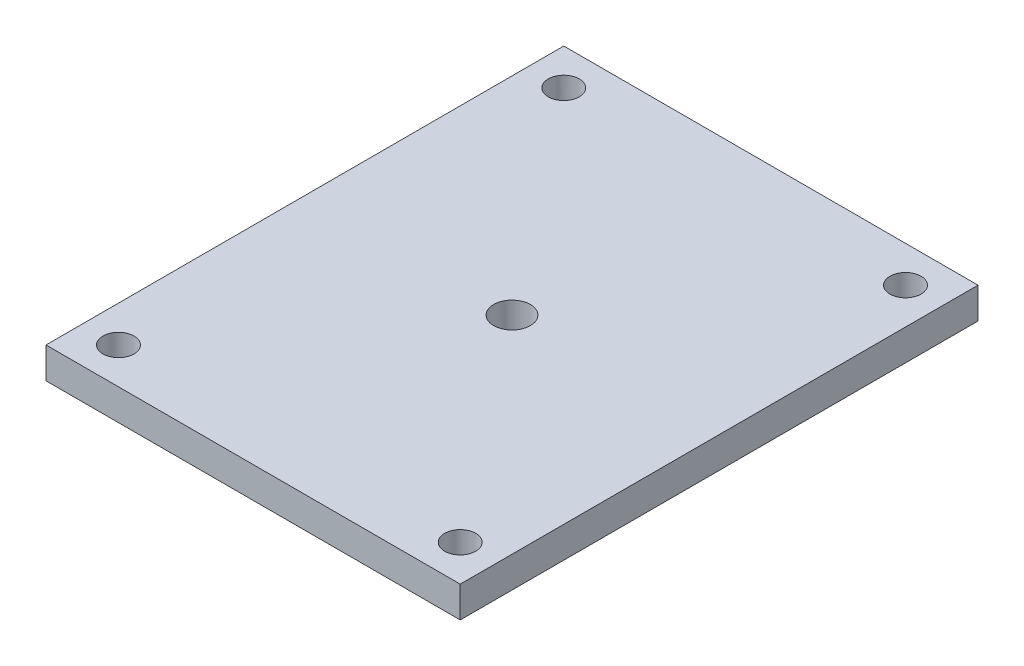
SolidWorks part; units mm, degrees
ref_plane "Alzado" through (0, 0, 0) normal (0, 0, 1) x (1, 0, 0)
ref_plane "Planta" through (0, 0, 0) normal (0, 1, 0) x (1, 0, 0)
ref_plane "Vista lateral" through (0, 0, 0) normal (1, 0, 0) x (0, 0, -1)
sketch "Croquis2" plane through (0, 0, 0) normal (0, 1, 0) x (1, 0, 0)
  line L1 (-254, -317.5) -> (254, -317.5)
  line L2 (-254, -317.5) -> (-254, 317.5)
  line L3 (-254, 317.5) -> (254, 317.5)
  line L4 (254, -317.5) -> (254, 317.5)
  line L5 (-254, -317.5) -> (254, 317.5) construction
  line L6 (-254, 317.5) -> (254, -317.5) construction
  point P0 (0, 0)
  dimension "D1" = 635
  dimension "D2" = 508
extrude "Saliente-Extruir2" add sketch "Croquis2" along normal blind 38.1
sketch "Croquis3" plane through (0, 38.1, 0) normal (0, 1, 0) x (1, 0, 0)
  line L0 (254, 317.5) -> (-254, 317.5) construction
  line L1 (-254, 317.5) -> (-254, -317.5) construction
  line L3 (0, 317.5) -> (0, -317.5) construction
  line L4 (-254, -317.5) -> (254, -317.5) construction
  line L5 (-254, 0) -> (254, 0) construction
  line L6 (254, -317.5) -> (254, 317.5) construction
  circle A0 centre (-209.55, 273.05) radius 19.05
  circle A1 centre (209.55, 273.05) radius 19.05
  circle A2 centre (209.55, -273.05) radius 19.05
  circle A3 centre (-209.55, -273.05) radius 19.05
  dimension "D1" = 38.1
  dimension "D3" = 44.45
  dimension "D2" = 44.45
extrude "Cortar-Extruir1" cut sketch "Croquis3" against normal up to surface (38.1 mm away) up to face at (0, 0, 0)
sketch "Croquis4" plane through (0, 38.1, 0) normal (0, 1, 0) x (1, 0, 0)
  line L0 (-254, 0) -> (254, 0) construction
  line L1 (-254, 317.5) -> (-254, -317.5) construction
  line L2 (254, -317.5) -> (254, 317.5) construction
  circle A0 centre (0, 0) radius 22.5
  dimension "D1" = 45
extrude "Cortar-Extruir2" cut sketch "Croquis4" against normal up to surface (38.1 mm away) up to face at (209.55, 0, -292.1)
